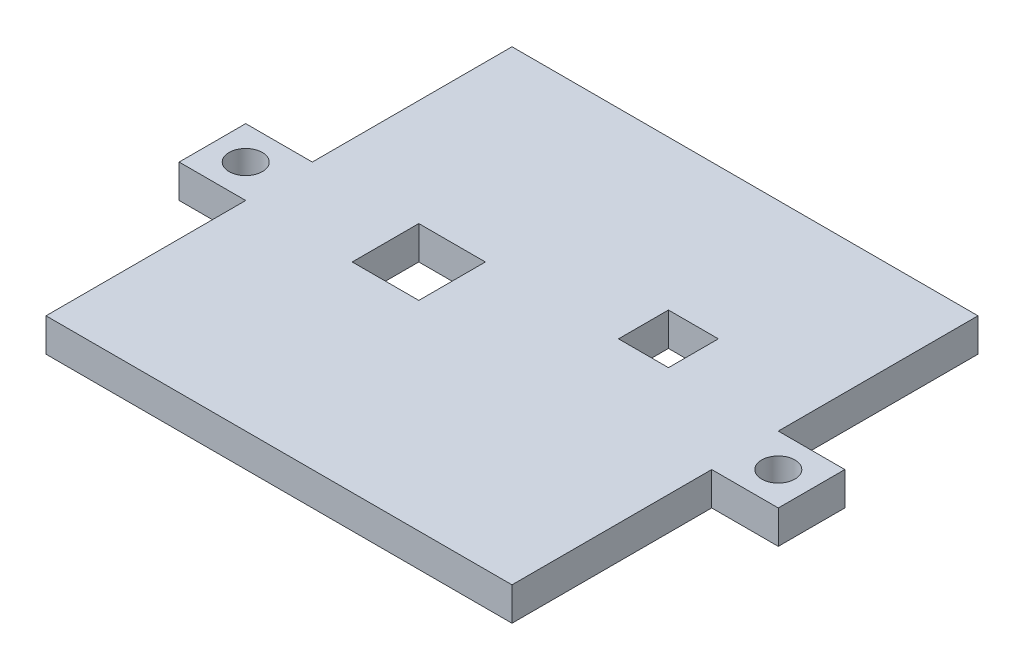
SolidWorks part; units mm, degrees
ref_plane "Front" through (0, 0, 0) normal (0, 0, 1) x (1, 0, 0)
ref_plane "Top" through (0, 0, 0) normal (0, 1, 0) x (1, 0, 0)
ref_plane "Right" through (0, 0, 0) normal (1, 0, 0) x (0, 0, -1)
sketch "Sketch1" plane through (0, 0, 0) normal (0, 1, 0) x (1, 0, 0)
  line L5 (-6.35, -6.35) -> (82.55, -6.35)
  line L6 (-6.35, -6.35) -> (-6.35, 82.55)
  line L7 (-6.35, 82.55) -> (82.55, 82.55)
  line L8 (82.55, -6.35) -> (82.55, 82.55)
  dimension "D1" = 88.9
  dimension "D2" = 6.35
  dimension "D3" = 88.9
  dimension "D4" = 6.35
extrude "Boss-Extrude1" add sketch "Sketch1" along normal blind 6.35
sketch "Sketch3" plane through (0, 6.35, 0) normal (0, 1, 0) x (1, 0, 0)
  line L0 (82.55, -6.35) -> (82.55, 82.55) construction
  line L1 (82.55, 44.45) -> (95.25, 44.45)
  line L2 (82.55, 44.45) -> (82.55, 31.75)
  line L3 (82.55, 31.75) -> (95.25, 31.75)
  line L4 (95.25, 44.45) -> (95.25, 31.75)
  line L5 (38.1, 82.55) -> (38.1, -6.35) construction
  line L6 (-6.35, 82.55) -> (-6.35, -6.35) construction
  line L8 (-19.05, 44.45) -> (-19.05, 31.75)
  line L9 (-6.35, 31.75) -> (-19.05, 31.75)
  line L10 (-6.35, 44.45) -> (-6.35, 31.75)
  line L11 (-6.35, 44.45) -> (-19.05, 44.45)
  line L12 (82.55, 82.55) -> (-6.35, 82.55) construction
  line L13 (-6.35, -6.35) -> (82.55, -6.35) construction
  point P6 (82.55, 38.1)
  point P7 (95.25, 38.1)
  point P18 (-19.05, 38.1)
  point P21 (-6.35, 38.1)
  dimension "D1" = 12.7
  dimension "D2" = 12.7
extrude "Boss-Extrude3" add sketch "Sketch3" against normal blind 6.35
sketch "Sketch4" plane through (0, 6.35, 0) normal (0, 1, 0) x (1, 0, 0)
  line L0 (38.1, 82.55) -> (38.1, -6.35) construction
  line L1 (95.25, 31.75) -> (95.25, 44.45) construction
  line L2 (-19.05, 44.45) -> (-19.05, 31.75) construction
  line L3 (82.55, 82.55) -> (-6.35, 82.55) construction
  line L4 (-6.35, -6.35) -> (82.55, -6.35) construction
  circle A0 centre (88.9, 38.1) radius 3.175
  circle A1 centre (-12.7, 38.1) radius 3.175
  point P10 (0, 0)
  point P13 (95.25, 38.1)
  point P14 (0, 0)
  point P17 (-19.05, 38.1)
  dimension "D1" = 6.35
extrude "Cut-Extrude1" cut sketch "Sketch4" against normal through all
sketch "Sketch6" plane through (0, 6.35, 0) normal (0, 1, 0) x (1, 0, 0)
  line L0 (-6.35, -6.35) -> (82.55, -6.35) construction
  line L1 (13.97, 44.45) -> (26.67, 44.45)
  line L2 (13.97, 44.45) -> (13.97, 31.75)
  line L3 (13.97, 31.75) -> (26.67, 31.75)
  line L4 (26.67, 44.45) -> (26.67, 31.75)
  line L5 (-6.35, 31.75) -> (-6.35, -6.35) construction
  line L7 (52.07, 53.975) -> (61.595, 53.975)
  line L8 (52.07, 53.975) -> (52.07, 44.45)
  line L9 (52.07, 44.45) -> (61.595, 44.45)
  line L10 (61.595, 53.975) -> (61.595, 44.45)
  point P8 (13.97, 38.1)
  dimension "D1" = 12.7
  dimension "D2" = 12.7
  dimension "D3" = 38.1
  dimension "D4" = 20.32
  dimension "D5" = 9.525
  dimension "D6" = 9.525
  dimension "D7" = 25.4
  dimension "D8" = 0
extrude "Cut-Extrude2" cut sketch "Sketch6" against normal blind 6.35
